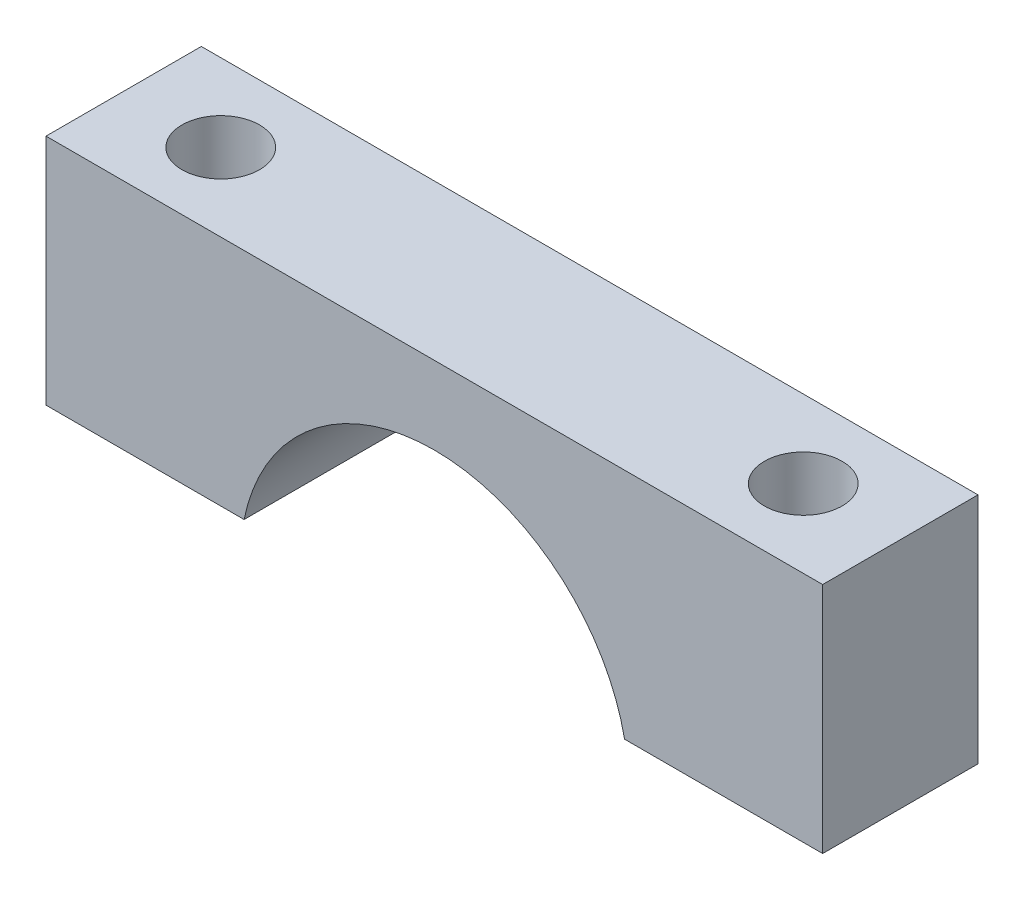
SolidWorks part; units mm, degrees
ref_plane "Front Plane" through (0, 0, 0) normal (0, 0, 1) x (1, 0, 0)
ref_plane "Top Plane" through (0, 0, 0) normal (0, 1, 0) x (1, 0, 0)
ref_plane "Right Plane" through (0, 0, 0) normal (1, 0, 0) x (0, 0, -1)
sketch "Sketch1" plane through (0, 0, 0) normal (0, 0, 1) x (1, 0, 0)
  line L0 (4.899, -3) -> (10, -3)
  line L1 (-10, 3) -> (10, 3)
  line L2 (-10, 3) -> (-10, -3)
  line L3 (-10, -3) -> (-4.899, -3)
  line L4 (10, 3) -> (10, -3)
  arc A0 (4.899, -3) -> (-4.899, -3) centre (0, -4) ccw
  point P4 (0, 3)
  point P6 (10, 0)
  dimension "D4" = 5
  dimension "D1" = 20
  dimension "D2" = 6
  dimension "D3" = 1
extrude "Extrude1" add sketch "Sketch1" along normal blind 4
sketch "Sketch2" plane through (0, -3, 0) normal (0, -1, 0) x (1, 0, 0)
  line L0 (-10, 4) -> (-10, 0) construction
  circle A0 centre (-7.5, 2) radius 1
  point P4 (-10, 2)
  dimension "D2" = 2
  dimension "D1" = 2.5
extrude "Extrude2" cut sketch "Sketch2" against normal through all
mirror "Mirror1" about plane through (0, 0, 0) normal (1, 0, 0) of "Extrude2"
